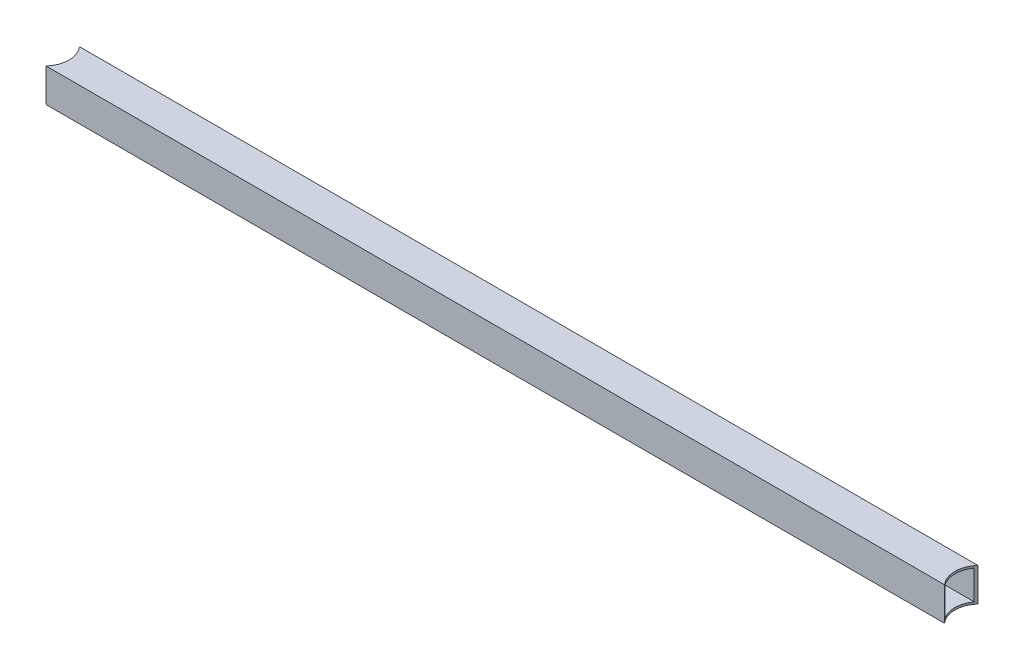
SolidWorks part; units mm, degrees
material "6061 Alloy"
ref_plane "Front Plane" through (0, 0, 0) normal (0, 0, 1) x (1, 0, 0)
ref_plane "Top Plane" through (0, 0, 0) normal (0, 1, 0) x (1, 0, 0)
ref_plane "Right Plane" through (0, 0, 0) normal (1, 0, 0) x (0, 0, -1)
sketch "Sketch1" plane through (0, 0, 0) normal (1, 0, 0) x (0, 0, -1)
  line L0 (0, 0) -> (1.5875, 1.5875) construction
  line L1 (0, 0) -> (25.4, 0)
  line L2 (0, 0) -> (0, 25.4)
  line L3 (0, 25.4) -> (25.4, 25.4)
  line L4 (25.4, 0) -> (25.4, 25.4)
  line L5 (1.5875, 1.5875) -> (23.8125, 1.5875)
  line L6 (1.5875, 1.5875) -> (1.5875, 23.8125)
  line L7 (1.5875, 23.8125) -> (23.8125, 23.8125)
  line L8 (23.8125, 1.5875) -> (23.8125, 23.8125)
  line L9 (23.8125, 23.8125) -> (25.4, 25.4) construction
  point P9 (0, 0)
  point P10 (23.6601, 1.7399)
  dimension "D1" = 25.4
  dimension "D2" = 25.4
  dimension "D3" = 1.5875
  dimension "D4" = 1.5875
extrude "Boss-Extrude1" add sketch "Sketch1" along normal blind 711.2
sketch "Sketch2" plane through (0, 25.4, 0) normal (0, 1, 0) x (1, 0, 0)
  line L0 (355.6, 0) -> (355.6, 25.4) construction
  line L1 (711.2, 0) -> (0, 0) construction
  line L2 (711.2, 25.4) -> (0, 25.4) construction
  line L3 (711.2, 12.7) -> (0, 12.7) construction
  line L4 (0, 25.4) -> (0, 0) construction
  circle A0 centre (0, 12.7) radius 19.05
  circle A1 centre (711.2, 12.7) radius 19.05
  point P11 (355.6, 12.7)
  dimension "D1" = 38.1
extrude "Cut-Extrude1" cut sketch "Sketch2" against normal through all
